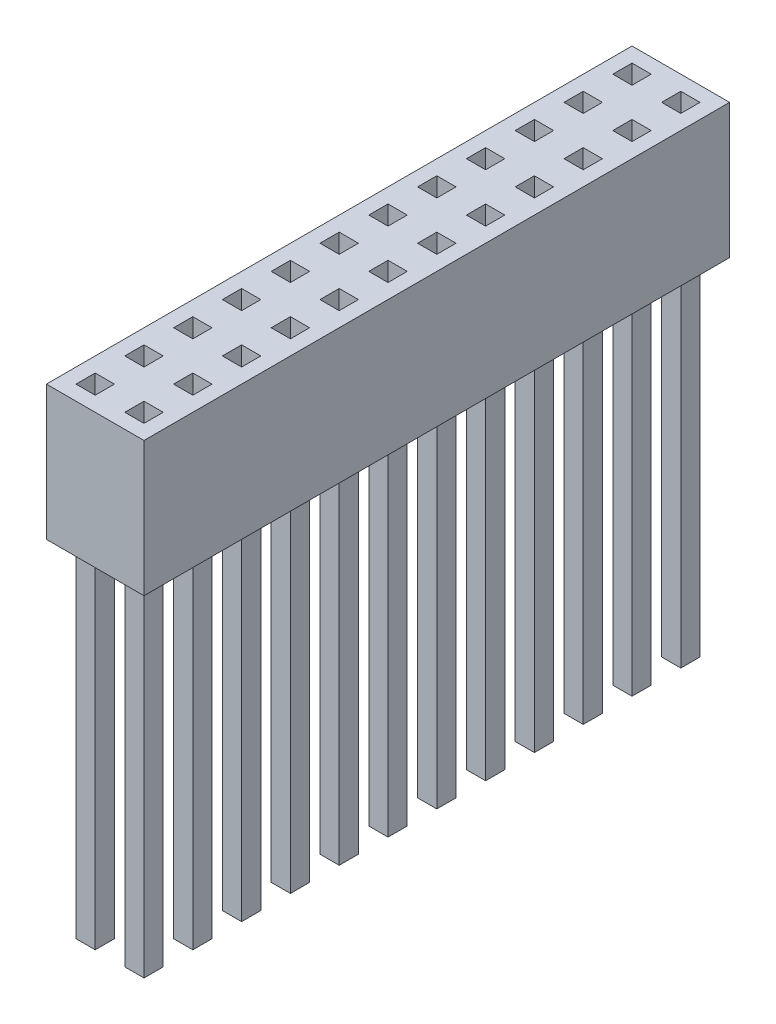
SolidWorks part; units mm, degrees
ref_plane "Спереди" through (0, 0, 0) normal (0, 0, 1) x (1, 0, 0)
ref_plane "Сверху" through (0, 0, 0) normal (0, 1, 0) x (1, 0, 0)
ref_plane "Справа" through (0, 0, 0) normal (1, 0, 0) x (0, 0, -1)
sketch "Эскиз1" plane through (0, 0, 0) normal (0, 1, 0) x (1, 0, 0)
  line L0 (2.04, 0.5) -> (3.04, 0.5)
  line L1 (-0.5, 0.5) -> (0.5, 0.5)
  line L2 (-0.5, 0.5) -> (-0.5, -0.5)
  line L3 (-0.5, -0.5) -> (0.5, -0.5)
  line L4 (0.5, 0.5) -> (0.5, -0.5)
  line L5 (-0.5, 0.5) -> (0.5, -0.5) construction
  line L6 (-0.5, -0.5) -> (0.5, 0.5) construction
  line L7 (2.04, 0.5) -> (2.04, -0.5)
  line L8 (2.04, -0.5) -> (3.04, -0.5)
  line L9 (3.04, 0.5) -> (3.04, -0.5)
  line L10 (2.04, 0.5) -> (3.04, -0.5) construction
  line L11 (2.04, -0.5) -> (3.04, 0.5) construction
  line L12 (2.04, 3.04) -> (3.04, 3.04)
  line L13 (2.04, 3.04) -> (2.04, 2.04)
  line L14 (2.04, 2.04) -> (3.04, 2.04)
  line L15 (3.04, 3.04) -> (3.04, 2.04)
  line L16 (2.04, 3.04) -> (3.04, 2.04) construction
  line L17 (2.04, 2.04) -> (3.04, 3.04) construction
  line L18 (2.04, 5.58) -> (3.04, 5.58)
  line L19 (2.04, 5.58) -> (2.04, 4.58)
  line L20 (2.04, 4.58) -> (3.04, 4.58)
  line L21 (3.04, 5.58) -> (3.04, 4.58)
  line L22 (2.04, 5.58) -> (3.04, 4.58) construction
  line L23 (2.04, 4.58) -> (3.04, 5.58) construction
  line L24 (2.04, 8.12) -> (3.04, 8.12)
  line L25 (2.04, 8.12) -> (2.04, 7.12)
  line L26 (2.04, 7.12) -> (3.04, 7.12)
  line L27 (3.04, 8.12) -> (3.04, 7.12)
  line L28 (2.04, 8.12) -> (3.04, 7.12) construction
  line L29 (2.04, 7.12) -> (3.04, 8.12) construction
  line L30 (2.04, 10.66) -> (3.04, 10.66)
  line L31 (2.04, 10.66) -> (2.04, 9.66)
  line L32 (2.04, 9.66) -> (3.04, 9.66)
  line L33 (3.04, 10.66) -> (3.04, 9.66)
  line L34 (2.04, 10.66) -> (3.04, 9.66) construction
  line L35 (2.04, 9.66) -> (3.04, 10.66) construction
  line L36 (2.04, 13.2) -> (3.04, 13.2)
  line L37 (2.04, 13.2) -> (2.04, 12.2)
  line L38 (2.04, 12.2) -> (3.04, 12.2)
  line L39 (3.04, 13.2) -> (3.04, 12.2)
  line L40 (2.04, 13.2) -> (3.04, 12.2) construction
  line L41 (2.04, 12.2) -> (3.04, 13.2) construction
  line L42 (2.04, 15.74) -> (3.04, 15.74)
  line L43 (2.04, 15.74) -> (2.04, 14.74)
  line L44 (2.04, 14.74) -> (3.04, 14.74)
  line L45 (3.04, 15.74) -> (3.04, 14.74)
  line L46 (2.04, 15.74) -> (3.04, 14.74) construction
  line L47 (2.04, 14.74) -> (3.04, 15.74) construction
  line L48 (2.04, 18.28) -> (3.04, 18.28)
  line L49 (2.04, 18.28) -> (2.04, 17.28)
  line L50 (2.04, 17.28) -> (3.04, 17.28)
  line L51 (3.04, 18.28) -> (3.04, 17.28)
  line L52 (2.04, 18.28) -> (3.04, 17.28) construction
  line L53 (2.04, 17.28) -> (3.04, 18.28) construction
  line L54 (2.04, 20.82) -> (3.04, 20.82)
  line L55 (2.04, 20.82) -> (2.04, 19.82)
  line L56 (2.04, 19.82) -> (3.04, 19.82)
  line L57 (3.04, 20.82) -> (3.04, 19.82)
  line L58 (2.04, 20.82) -> (3.04, 19.82) construction
  line L59 (2.04, 19.82) -> (3.04, 20.82) construction
  line L60 (2.04, 23.36) -> (3.04, 23.36)
  line L61 (2.04, 23.36) -> (2.04, 22.36)
  line L62 (2.04, 22.36) -> (3.04, 22.36)
  line L63 (3.04, 23.36) -> (3.04, 22.36)
  line L64 (2.04, 23.36) -> (3.04, 22.36) construction
  line L65 (2.04, 22.36) -> (3.04, 23.36) construction
  line L66 (2.04, 25.9) -> (3.04, 25.9)
  line L67 (2.04, 25.9) -> (2.04, 24.9)
  line L68 (2.04, 24.9) -> (3.04, 24.9)
  line L69 (3.04, 25.9) -> (3.04, 24.9)
  line L70 (2.04, 25.9) -> (3.04, 24.9) construction
  line L71 (2.04, 24.9) -> (3.04, 25.9) construction
  line L72 (2.04, 28.44) -> (3.04, 28.44)
  line L73 (2.04, 28.44) -> (2.04, 27.44)
  line L74 (2.04, 27.44) -> (3.04, 27.44)
  line L75 (3.04, 28.44) -> (3.04, 27.44)
  line L76 (2.04, 28.44) -> (3.04, 27.44) construction
  line L77 (2.04, 27.44) -> (3.04, 28.44) construction
  line L78 (-0.5, 3.04) -> (0.5, 3.04)
  line L79 (-0.5, 3.04) -> (-0.5, 2.04)
  line L80 (-0.5, 2.04) -> (0.5, 2.04)
  line L81 (0.5, 3.04) -> (0.5, 2.04)
  line L82 (-0.5, 3.04) -> (0.5, 2.04) construction
  line L83 (-0.5, 2.04) -> (0.5, 3.04) construction
  line L84 (-0.5, 5.58) -> (0.5, 5.58)
  line L85 (-0.5, 5.58) -> (-0.5, 4.58)
  line L86 (-0.5, 4.58) -> (0.5, 4.58)
  line L87 (0.5, 5.58) -> (0.5, 4.58)
  line L88 (-0.5, 5.58) -> (0.5, 4.58) construction
  line L89 (-0.5, 4.58) -> (0.5, 5.58) construction
  line L90 (-0.5, 8.12) -> (0.5, 8.12)
  line L91 (-0.5, 8.12) -> (-0.5, 7.12)
  line L92 (-0.5, 7.12) -> (0.5, 7.12)
  line L93 (0.5, 8.12) -> (0.5, 7.12)
  line L94 (-0.5, 8.12) -> (0.5, 7.12) construction
  line L95 (-0.5, 7.12) -> (0.5, 8.12) construction
  line L96 (-0.5, 10.66) -> (0.5, 10.66)
  line L97 (-0.5, 10.66) -> (-0.5, 9.66)
  line L98 (-0.5, 9.66) -> (0.5, 9.66)
  line L99 (0.5, 10.66) -> (0.5, 9.66)
  line L100 (-0.5, 10.66) -> (0.5, 9.66) construction
  line L101 (-0.5, 9.66) -> (0.5, 10.66) construction
  line L102 (-0.5, 13.2) -> (0.5, 13.2)
  line L103 (-0.5, 13.2) -> (-0.5, 12.2)
  line L104 (-0.5, 12.2) -> (0.5, 12.2)
  line L105 (0.5, 13.2) -> (0.5, 12.2)
  line L106 (-0.5, 13.2) -> (0.5, 12.2) construction
  line L107 (-0.5, 12.2) -> (0.5, 13.2) construction
  line L108 (-0.5, 15.74) -> (0.5, 15.74)
  line L109 (-0.5, 15.74) -> (-0.5, 14.74)
  line L110 (-0.5, 14.74) -> (0.5, 14.74)
  line L111 (0.5, 15.74) -> (0.5, 14.74)
  line L112 (-0.5, 15.74) -> (0.5, 14.74) construction
  line L113 (-0.5, 14.74) -> (0.5, 15.74) construction
  line L114 (-0.5, 18.28) -> (0.5, 18.28)
  line L115 (-0.5, 18.28) -> (-0.5, 17.28)
  line L116 (-0.5, 17.28) -> (0.5, 17.28)
  line L117 (0.5, 18.28) -> (0.5, 17.28)
  line L118 (-0.5, 18.28) -> (0.5, 17.28) construction
  line L119 (-0.5, 17.28) -> (0.5, 18.28) construction
  line L120 (-0.5, 20.82) -> (0.5, 20.82)
  line L121 (-0.5, 20.82) -> (-0.5, 19.82)
  line L122 (-0.5, 19.82) -> (0.5, 19.82)
  line L123 (0.5, 20.82) -> (0.5, 19.82)
  line L124 (-0.5, 20.82) -> (0.5, 19.82) construction
  line L125 (-0.5, 19.82) -> (0.5, 20.82) construction
  line L126 (-0.5, 23.36) -> (0.5, 23.36)
  line L127 (-0.5, 23.36) -> (-0.5, 22.36)
  line L128 (-0.5, 22.36) -> (0.5, 22.36)
  line L129 (0.5, 23.36) -> (0.5, 22.36)
  line L130 (-0.5, 23.36) -> (0.5, 22.36) construction
  line L131 (-0.5, 22.36) -> (0.5, 23.36) construction
  line L132 (-0.5, 25.9) -> (0.5, 25.9)
  line L133 (-0.5, 25.9) -> (-0.5, 24.9)
  line L134 (-0.5, 24.9) -> (0.5, 24.9)
  line L135 (0.5, 25.9) -> (0.5, 24.9)
  line L136 (-0.5, 25.9) -> (0.5, 24.9) construction
  line L137 (-0.5, 24.9) -> (0.5, 25.9) construction
  line L138 (-0.5, 28.44) -> (0.5, 28.44)
  line L139 (-0.5, 28.44) -> (-0.5, 27.44)
  line L140 (-0.5, 27.44) -> (0.5, 27.44)
  line L141 (0.5, 28.44) -> (0.5, 27.44)
  line L142 (-0.5, 28.44) -> (0.5, 27.44) construction
  line L143 (-0.5, 27.44) -> (0.5, 28.44) construction
  point P0 (0, 0)
  point P8 (2.54, 0)
  point P13 (2.54, 2.54)
  point P18 (2.54, 5.08)
  point P23 (2.54, 7.62)
  point P28 (2.54, 10.16)
  point P33 (2.54, 12.7)
  point P38 (2.54, 15.24)
  point P43 (2.54, 17.78)
  point P48 (2.54, 20.32)
  point P53 (2.54, 22.86)
  point P58 (2.54, 25.4)
  point P63 (2.54, 27.94)
  point P68 (0, 2.54)
  point P73 (0, 5.08)
  point P78 (0, 7.62)
  point P83 (0, 10.16)
  point P88 (0, 12.7)
  point P93 (0, 15.24)
  point P98 (0, 17.78)
  point P103 (0, 20.32)
  point P108 (0, 22.86)
  point P113 (0, 25.4)
  point P118 (0, 27.94)
  dimension "D1" = 2
  dimension "D2" = 12
extrude "Бобышка-Вытянуть1" add sketch "Эскиз1" along normal blind 20 and the other way blind 4
sketch "Эскиз2" plane through (0, 20, 0) normal (0, 1, 0) x (1, 0, 0)
  line L0 (2.04, -0.5) -> (3.04, -0.5)
  line L1 (-1.27, -1.27) -> (3.81, -1.27)
  line L2 (-1.27, -1.27) -> (-1.27, 29.21)
  line L3 (-1.27, 29.21) -> (3.81, 29.21)
  line L4 (3.81, -1.27) -> (3.81, 29.21)
  line L5 (-0.5, -0.5) -> (0.5, -0.5)
  line L6 (-0.5, -0.5) -> (-0.5, 0.5)
  line L7 (-0.5, 0.5) -> (0.5, 0.5)
  line L8 (0.5, -0.5) -> (0.5, 0.5)
  line L13 (2.04, -0.5) -> (2.04, 0.5)
  line L14 (2.04, 0.5) -> (3.04, 0.5)
  line L15 (3.04, -0.5) -> (3.04, 0.5)
  line L16 (2.04, 2.04) -> (3.04, 2.04)
  line L17 (2.04, 2.04) -> (2.04, 3.04)
  line L18 (2.04, 3.04) -> (3.04, 3.04)
  line L19 (3.04, 2.04) -> (3.04, 3.04)
  line L20 (2.04, 4.58) -> (3.04, 4.58)
  line L21 (2.04, 4.58) -> (2.04, 5.58)
  line L22 (2.04, 5.58) -> (3.04, 5.58)
  line L23 (3.04, 4.58) -> (3.04, 5.58)
  line L24 (2.04, 7.12) -> (3.04, 7.12)
  line L25 (2.04, 7.12) -> (2.04, 8.12)
  line L26 (2.04, 8.12) -> (3.04, 8.12)
  line L27 (3.04, 7.12) -> (3.04, 8.12)
  line L28 (2.04, 9.66) -> (3.04, 9.66)
  line L29 (2.04, 9.66) -> (2.04, 10.66)
  line L30 (2.04, 10.66) -> (3.04, 10.66)
  line L31 (3.04, 9.66) -> (3.04, 10.66)
  line L32 (2.04, 12.2) -> (3.04, 12.2)
  line L33 (2.04, 12.2) -> (2.04, 13.2)
  line L34 (2.04, 13.2) -> (3.04, 13.2)
  line L35 (3.04, 12.2) -> (3.04, 13.2)
  line L36 (2.04, 14.74) -> (3.04, 14.74)
  line L37 (2.04, 14.74) -> (2.04, 15.74)
  line L38 (2.04, 15.74) -> (3.04, 15.74)
  line L39 (3.04, 14.74) -> (3.04, 15.74)
  line L40 (2.04, 17.28) -> (3.04, 17.28)
  line L41 (2.04, 17.28) -> (2.04, 18.28)
  line L42 (2.04, 18.28) -> (3.04, 18.28)
  line L43 (3.04, 17.28) -> (3.04, 18.28)
  line L44 (2.04, 19.82) -> (3.04, 19.82)
  line L45 (2.04, 19.82) -> (2.04, 20.82)
  line L46 (2.04, 20.82) -> (3.04, 20.82)
  line L47 (3.04, 19.82) -> (3.04, 20.82)
  line L48 (2.04, 22.36) -> (3.04, 22.36)
  line L49 (2.04, 22.36) -> (2.04, 23.36)
  line L50 (2.04, 23.36) -> (3.04, 23.36)
  line L51 (3.04, 22.36) -> (3.04, 23.36)
  line L52 (2.04, 24.9) -> (3.04, 24.9)
  line L53 (2.04, 24.9) -> (2.04, 25.9)
  line L54 (2.04, 25.9) -> (3.04, 25.9)
  line L55 (3.04, 24.9) -> (3.04, 25.9)
  line L56 (2.04, 27.44) -> (3.04, 27.44)
  line L57 (2.04, 27.44) -> (2.04, 28.44)
  line L58 (2.04, 28.44) -> (3.04, 28.44)
  line L59 (3.04, 27.44) -> (3.04, 28.44)
  line L60 (-0.5, 2.04) -> (0.5, 2.04)
  line L61 (-0.5, 2.04) -> (-0.5, 3.04)
  line L62 (-0.5, 3.04) -> (0.5, 3.04)
  line L63 (0.5, 2.04) -> (0.5, 3.04)
  line L64 (-0.5, 4.58) -> (0.5, 4.58)
  line L65 (-0.5, 4.58) -> (-0.5, 5.58)
  line L66 (-0.5, 5.58) -> (0.5, 5.58)
  line L67 (0.5, 4.58) -> (0.5, 5.58)
  line L68 (-0.5, 7.12) -> (0.5, 7.12)
  line L69 (-0.5, 7.12) -> (-0.5, 8.12)
  line L70 (-0.5, 8.12) -> (0.5, 8.12)
  line L71 (0.5, 7.12) -> (0.5, 8.12)
  line L72 (-0.5, 9.66) -> (0.5, 9.66)
  line L73 (-0.5, 9.66) -> (-0.5, 10.66)
  line L74 (-0.5, 10.66) -> (0.5, 10.66)
  line L75 (0.5, 9.66) -> (0.5, 10.66)
  line L76 (-0.5, 12.2) -> (0.5, 12.2)
  line L77 (-0.5, 12.2) -> (-0.5, 13.2)
  line L78 (-0.5, 13.2) -> (0.5, 13.2)
  line L79 (0.5, 12.2) -> (0.5, 13.2)
  line L80 (-0.5, 14.74) -> (0.5, 14.74)
  line L81 (-0.5, 14.74) -> (-0.5, 15.74)
  line L82 (-0.5, 15.74) -> (0.5, 15.74)
  line L83 (0.5, 14.74) -> (0.5, 15.74)
  line L84 (-0.5, 17.28) -> (0.5, 17.28)
  line L85 (-0.5, 17.28) -> (-0.5, 18.28)
  line L86 (-0.5, 18.28) -> (0.5, 18.28)
  line L87 (0.5, 17.28) -> (0.5, 18.28)
  line L88 (-0.5, 19.82) -> (0.5, 19.82)
  line L89 (-0.5, 19.82) -> (-0.5, 20.82)
  line L90 (-0.5, 20.82) -> (0.5, 20.82)
  line L91 (0.5, 19.82) -> (0.5, 20.82)
  line L92 (-0.5, 22.36) -> (0.5, 22.36)
  line L93 (-0.5, 22.36) -> (-0.5, 23.36)
  line L94 (-0.5, 23.36) -> (0.5, 23.36)
  line L95 (0.5, 22.36) -> (0.5, 23.36)
  line L96 (-0.5, 24.9) -> (0.5, 24.9)
  line L97 (-0.5, 24.9) -> (-0.5, 25.9)
  line L98 (-0.5, 25.9) -> (0.5, 25.9)
  line L99 (0.5, 24.9) -> (0.5, 25.9)
  line L100 (-0.5, 27.44) -> (0.5, 27.44)
  line L101 (-0.5, 27.44) -> (-0.5, 28.44)
  line L102 (-0.5, 28.44) -> (0.5, 28.44)
  line L103 (0.5, 27.44) -> (0.5, 28.44)
  dimension "D1" = 2
  dimension "D2" = 12
extrude "Бобышка-Вытянуть2" add sketch "Эскиз2" along normal blind 1 and the other way blind 6
